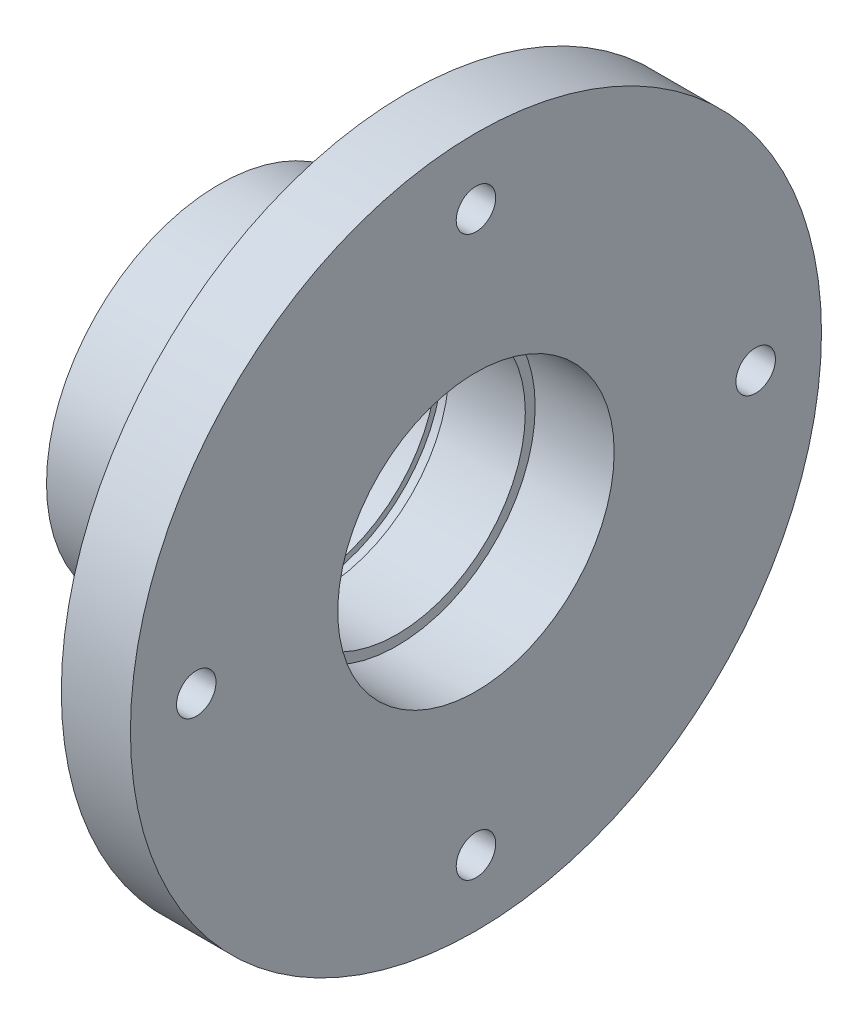
SolidWorks part; units mm, degrees
ref_plane "Front Plane" through (0, 0, 0) normal (0, 0, 1) x (1, 0, 0)
ref_plane "Top Plane" through (0, 0, 0) normal (0, 1, 0) x (1, 0, 0)
ref_plane "Right Plane" through (0, 0, 0) normal (1, 0, 0) x (0, 0, -1)
sketch "Sketch1" plane through (0, 0, 0) normal (1, 0, 0) x (0, 0, -1)
  circle A0 centre (0, 0) radius 35
extrude "Boss-Extrude1" add sketch "Sketch1" against normal blind 26
sketch "Sketch2" plane through (-26, 0, 0) normal (-1, 0, 0) x (0, 0, 1)
  circle A0 centre (0, 0) radius 17.5
  circle A1 centre (0, 0) radius 35
extrude "Cut-Extrude1" cut sketch "Sketch2" against normal blind 19
sketch "Sketch3" plane through (-7, 0, 0) normal (-1, 0, 0) x (0, 0, 1)
  circle A0 centre (0, 28.33) radius 2
  circle A1 centre (28.33, 0) radius 2
  circle A2 centre (0, -28.33) radius 2
  circle A3 centre (-28.33, 0) radius 2
  point P12 (0, 0)
  dimension "D1" = 28.33
  dimension "D2" = 4
extrude "Cut-Extrude2" cut sketch "Sketch3" against normal blind 18
sketch "Sketch4" plane through (-7, 0, 0) normal (-1, 0, 0) x (0, 0, 1)
  circle A0 centre (0, 28.33) radius 5.5
  circle A1 centre (28.33, 0) radius 5.5
  circle A2 centre (0, -28.33) radius 5.5
  circle A3 centre (-28.33, 0) radius 5.5
  point P12 (0, 0)
  dimension "D1" = 4
extrude "Cut-Extrude4" cut sketch "Sketch4" against normal blind 3
sketch "Sketch5" plane through (-26, 0, 0) normal (-1, 0, 0) x (0, 0, 1)
  circle A0 centre (0, 0) radius 9.5
extrude "Cut-Extrude5" cut sketch "Sketch5" against normal up to next
sketch "Sketch6" plane through (0, 0, 0) normal (1, 0, 0) x (0, 0, -1)
  circle A0 centre (0, 0) radius 13
  dimension "D1" = 26
extrude "Cut-Extrude6" cut sketch "Sketch6" against normal blind 22
ref_plane "Plane1" through (0, 17.5, 0) normal (0, 1, 0) x (1, 0, 0)
sketch "Sketch7" plane through (0, 17.5, 0) normal (0, 1, 0) x (1, 0, 0)
  line L0 (-26, 17.5) -> (-26, -17.5) construction
  circle A0 centre (-11, 0) radius 2.5
  dimension "D1" = 15
extrude "Cut-Extrude7" cut sketch "Sketch7" against normal up to next
sketch "Sketch8" plane through (0, 0, 0) normal (1, 0, 0) x (0, 0, -1)
  circle A0 centre (0, 0) radius 14
extrude "Cut-Extrude8" cut sketch "Sketch8" against normal blind 8
ref_plane "Plane2" through (-16.35, 0, 0) normal (1, 0, 0) x (0, 0, -1)
sketch "Sketch9" plane through (-16.35, 0, 0) normal (1, 0, 0) x (0, 0, -1)
  circle A0 centre (0, 0) radius 13.6
extrude "Cut-Extrude9" cut sketch "Sketch9" against normal mid plane 1.25
